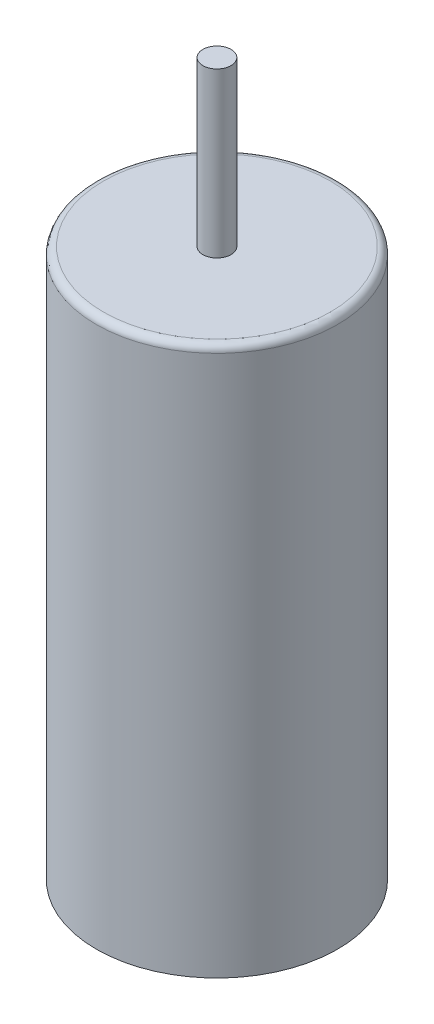
SolidWorks part; units mm, degrees
ref_plane "Front Plane" through (0, 0, 0) normal (0, 0, 1) x (1, 0, 0)
ref_plane "Top Plane" through (0, 0, 0) normal (0, 1, 0) x (1, 0, 0)
ref_plane "Right Plane" through (0, 0, 0) normal (1, 0, 0) x (0, 0, -1)
sketch "Sketch1" plane through (0, 0, 0) normal (0, 1, 0) x (1, 0, 0)
  circle A0 centre (0, 0) radius 4.25
  dimension "D1" = 8.5
extrude "Boss-Extrude1" add sketch "Sketch1" along normal mid plane 19.304
sketch "Sketch2" plane through (0, 9.652, 0) normal (0, 1, 0) x (1, 0, 0)
  circle A0 centre (0, 0) radius 0.4953
  dimension "D1" = 0.9906
extrude "Boss-Extrude2" add sketch "Sketch2" along normal blind 5.7658
fillet "Fillet1" radius 0.254 1 edges at (0, 9.652, 4.25)
